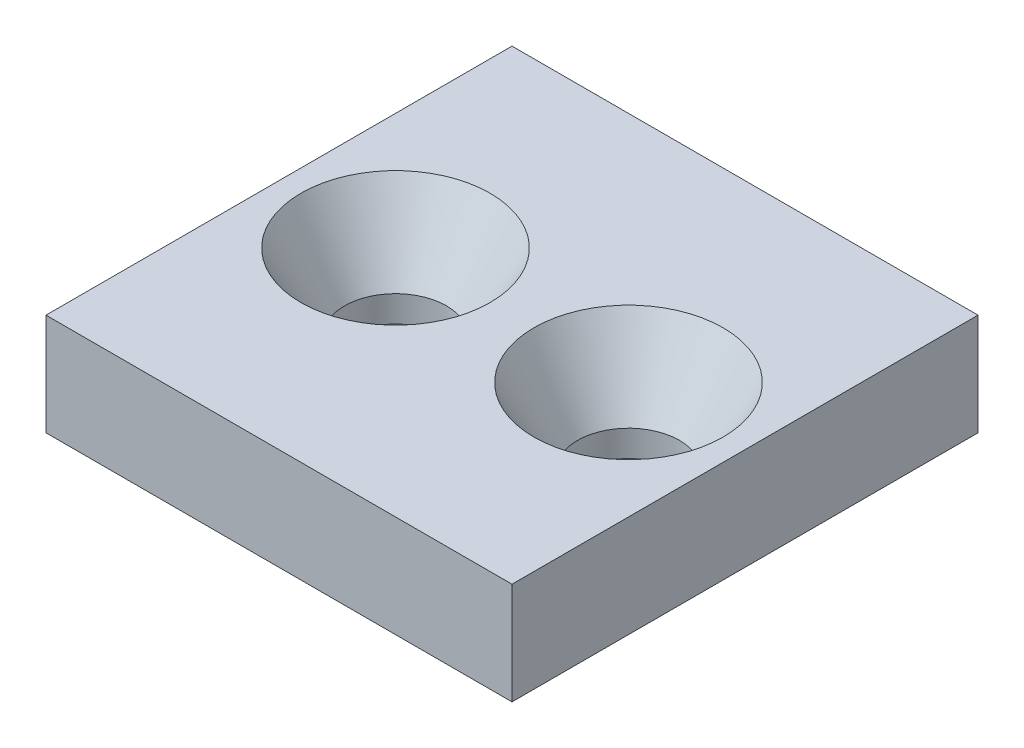
SolidWorks part; units mm, degrees
ref_plane "Front Plane" through (0, 0, 0) normal (0, 0, 1) x (1, 0, 0)
ref_plane "Top Plane" through (0, 0, 0) normal (0, 1, 0) x (1, 0, 0)
ref_plane "Right Plane" through (0, 0, 0) normal (1, 0, 0) x (0, 0, -1)
sketch "Sketch2" plane through (0, 0, 0) normal (0, 1, 0) x (1, 0, 0)
  line L0 (0, 16) -> (32, 16) construction
  line L1 (0, 0) -> (32, 0)
  line L2 (0, 0) -> (0, 32)
  line L3 (0, 32) -> (32, 32)
  line L4 (32, 0) -> (32, 32)
  circle A0 centre (8, 16) radius 3.5
  circle A2 centre (24, 16) radius 3.5
  dimension "D5" = 7
  dimension "D6" = 7
  dimension "D1" = 32
  dimension "D2" = 32
  dimension "D3" = 8
  dimension "D4" = 8
extrude "Boss-Extrude1" add sketch "Sketch2" along normal blind 7
chamfer "Chamfer2" distance 3 angle 60 1 edges at (24, 7, -12.5)
chamfer "Chamfer3" distance 3 angle 60 1 edges at (8, 7, -12.5)
